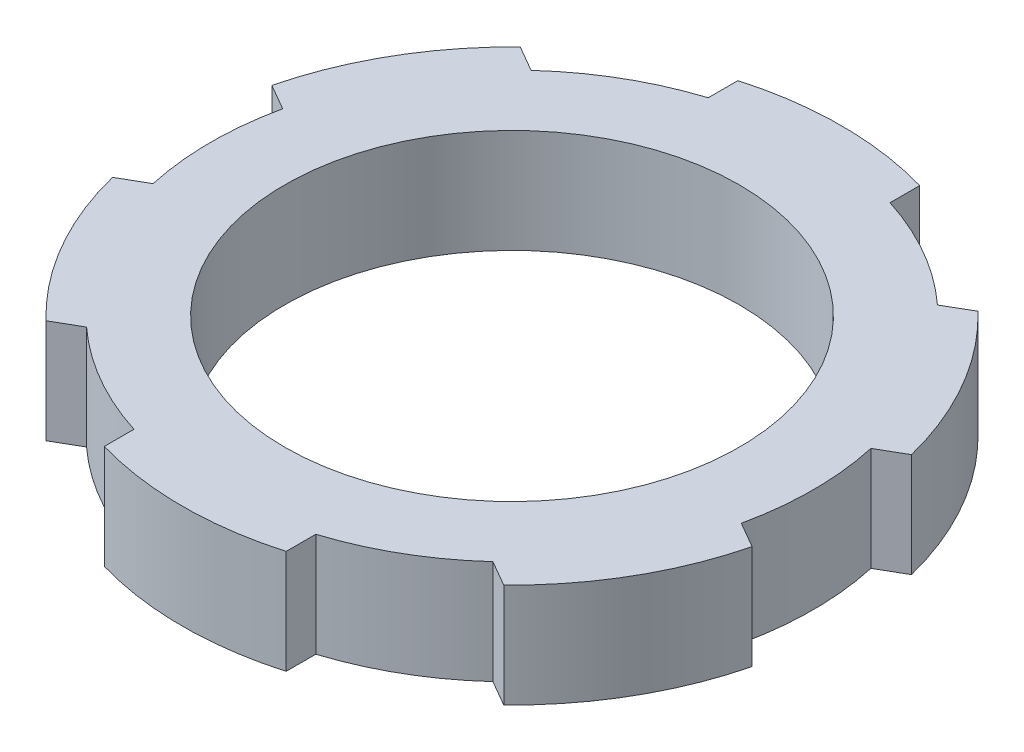
SolidWorks part; units mm, degrees
ref_plane "Front" through (0, 0, 0) normal (0, 0, 1) x (1, 0, 0)
ref_plane "Top" through (0, 0, 0) normal (0, 1, 0) x (1, 0, 0)
ref_plane "Right" through (0, 0, 0) normal (1, 0, 0) x (0, 0, -1)
sketch "Sketch1" plane through (0, 0, 0) normal (0, 1, 0) x (1, 0, 0)
  circle A0 centre (0, 0) radius 10
  circle A1 centre (0, 0) radius 13.25
  point P31 (0, 0)
  dimension "D1" = 20
  dimension "D2" = 26.5
extrude "Boss-Extrude1" add sketch "Sketch1" along normal blind 4.572
sketch "Sketch2" plane through (0, 4.572, 0) normal (0, 1, 0) x (1, 0, 0)
  line L0 (0, 0) -> (0, 14.5) construction
  line L1 (-4, 12.6318) -> (-4, 13.9374)
  line L2 (4, 13.9374) -> (4, 12.6318)
  arc A0 (4, 12.6318) -> (-4, 12.6318) centre (0, 0) ccw
  arc A2 (4, 13.9374) -> (-4, 13.9374) centre (0, 0) ccw
  circle A3 centre (0, 0) radius 13.25 construction
  dimension "D1" = 29
  dimension "D2" = 8
extrude "Boss-Extrude2" add sketch "Sketch2" against normal up to surface (4.572 mm away) up to face at (0, 0, 13.25)
pattern_circular "CirPattern1" count 6 over 360 about axis through (0, 0, 0) along (0, 1, 0) of "Boss-Extrude2"
